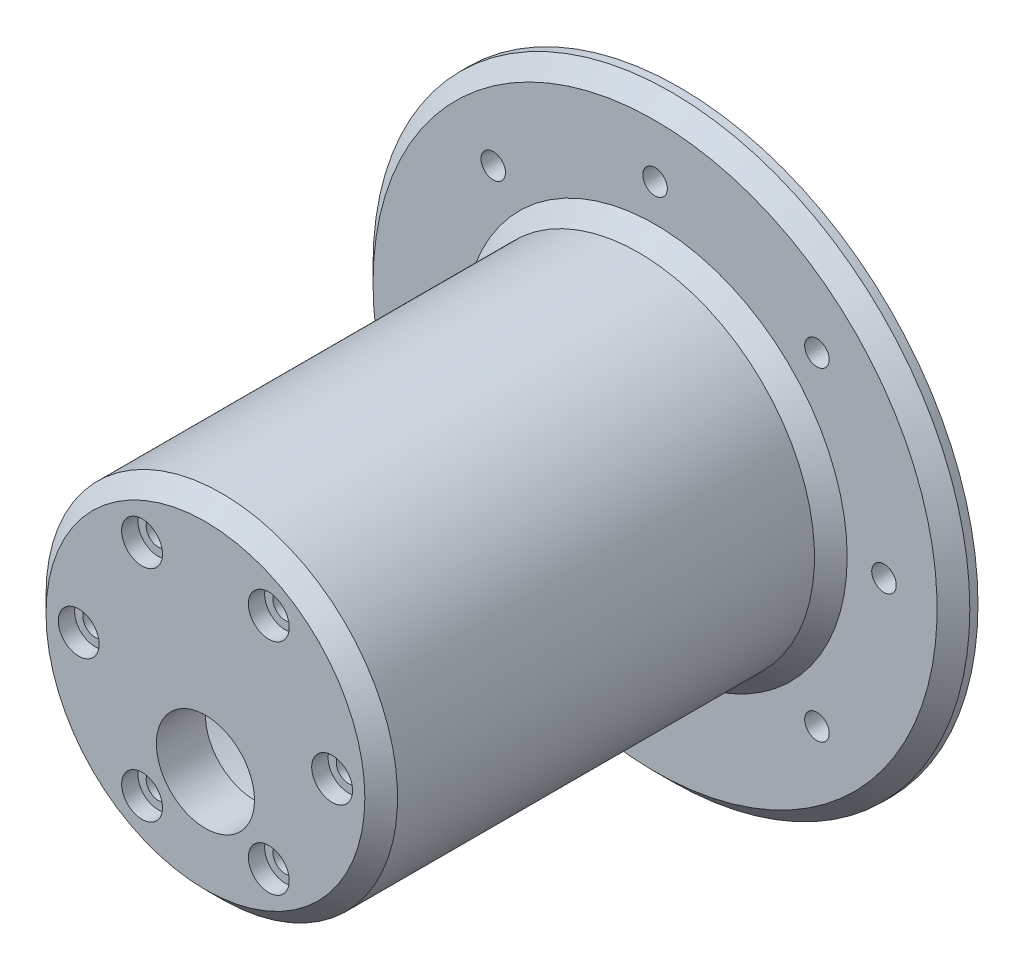
SolidWorks part; units mm, degrees
material "2014 Alloy"
ref_plane "Front Plane" through (0, 0, 0) normal (0, 0, 1) x (1, 0, 0)
ref_plane "Top Plane" through (0, 0, 0) normal (0, 1, 0) x (1, 0, 0)
ref_plane "Right Plane" through (0, 0, 0) normal (1, 0, 0) x (0, 0, -1)
sketch "Sketch1" plane through (0, 0, 0) normal (1, 0, 0) x (0, 0, -1)
  line L0 (0, 0) -> (0, 18.5)
  line L1 (0, 18.5) -> (52, 18.5)
  line L2 (52, 18.5) -> (52, 23.5)
  line L3 (49, 21.5) -> (-6, 21.5)
  line L4 (-6, 21.5) -> (-6, 0)
  line L5 (-6, 0) -> (0, 0)
  line L6 (52, 23.5) -> (51, 23.5)
  line L7 (51, 23.5) -> (51, 25.5)
  line L8 (52, 36.5) -> (49, 36.5)
  line L9 (49, 36.5) -> (49, 21.5)
  line L10 (51, 25.5) -> (52, 25.5)
  line L11 (52, 25.5) -> (52, 36.5)
  dimension "D1" = 18.5
  dimension "D2" = 6
  dimension "D3" = 3
  dimension "D4" = 55
  dimension "D5" = 3
  dimension "D6" = 15
  dimension "D7" = 5
  dimension "D8" = 1
  dimension "D9" = 2
revolve "Revolve1" add sketch "Sketch1" angle 360 about L5
sketch "Sketch2" plane through (0, 0, 6) normal (0, 0, 1) x (1, 0, 0)
  line L0 (0, 0) -> (21.5, 0) construction
  circle A0 centre (0, 0) radius 21.5 construction
hole_wizard "CBORE for M1.6 Hex Head Cap Screw1" positions "Sketch4" profile "Sketch3" counterbore size "M1.6" standard "ISO" end condition through all
sketch "Sketch4" plane through (0, 0, 6) normal (0, 0, 1) x (1, 0, 0)
  point P0 (15.5, 0)
  dimension "D1" = 15.5
sketch "Sketch3" plane through (15.5, 0, 6) normal (1, 0, 0) x (0, -1, 0)
  line L0 (0, 0) -> (0, 58)
  line L1 (0, 58) -> (1.5, 58)
  line L3 (1.5, 58) -> (1.5, 2)
  line L4 (1.5, 2) -> (2.5, 2)
  line L5 (2.5, 2) -> (2.5, 0)
  line L7 (2.5, 0) -> (0, 0)
  line L11 (0, -6.35) -> (0, 107.95) construction
  dimension "Thru Hole Dia." = 3
  dimension "Thru Hole Depth" = 58
  dimension "C'Bore Dia." = 5
  dimension "C'Bore Depth" = 2
pattern_circular "CirPattern1" count 6 over 360 about axis through (0, 0, 0) along (0, 0, 1) of "CBORE for M1.6 Hex Head Cap Screw1"
hole_wizard "Ø12.0mm Dowel Hole1" positions "Sketch6" profile "Sketch5" hole size "Ø12.0" standard "ISO"
sketch "Sketch6" plane through (0, 0, 6) normal (0, 0, 1) x (1, 0, 0)
  point P0 (0, -7)
  dimension "D1" = 7
sketch "Sketch5" plane through (0, -7, 6) normal (1, 0, 0) x (0, -1, 0)
  line L0 (0, 0) -> (0, 18.6052)
  line L1 (0, 18.6052) -> (6, 15)
  line L2 (6, 15) -> (6, 0)
  line L5 (6, 0) -> (0, 0)
  line L10 (0, 18.6052) -> (-6, 15) construction
  line L11 (0, -6.35) -> (0, 107.95) construction
  dimension "Hole Dia." = 12
  dimension "Hole Depth" = 15
  dimension "Drill Angle" = 118
chamfer "Chamfer1" distance 2 angle 45 3 edges at (21.5, 0, 6) (36.5, 0, -49) (21.5, 0, -49)
hole_wizard "Ø3.0mm Dowel Hole3" positions "Sketch8" profile "Sketch7" hole size "Ø3.0" standard "ISO"
sketch "Sketch8" plane through (0, 0, -49) normal (0, 0, 1) x (1, 0, 0)
  circle A0 centre (0, 0) radius 21.5 construction
  point P0 (0, 28)
  dimension "D1" = 28
sketch "Sketch7" plane through (0, 28, -49) normal (1, 0, 0) x (0, -1, 0)
  line L0 (0, 0) -> (0, 15.9013)
  line L1 (0, 15.9013) -> (1.5, 15)
  line L2 (1.5, 15) -> (1.5, 0)
  line L5 (1.5, 0) -> (0, 0)
  line L10 (0, 15.9013) -> (-1.5, 15) construction
  line L11 (0, -6.35) -> (0, 107.95) construction
  dimension "Hole Dia." = 3
  dimension "Hole Depth" = 15
  dimension "Drill Angle" = 118
pattern_circular "CirPattern2" count 8 over 360 about axis through (0, 0, 0) along (0, 0, 1) of "Ø3.0mm Dowel Hole3"
sketch "Sketch9" plane through (0, 0, -49) normal (0, 0, 1) x (1, 0, 0)
  circle A0 centre (0, 0) radius 28 construction
